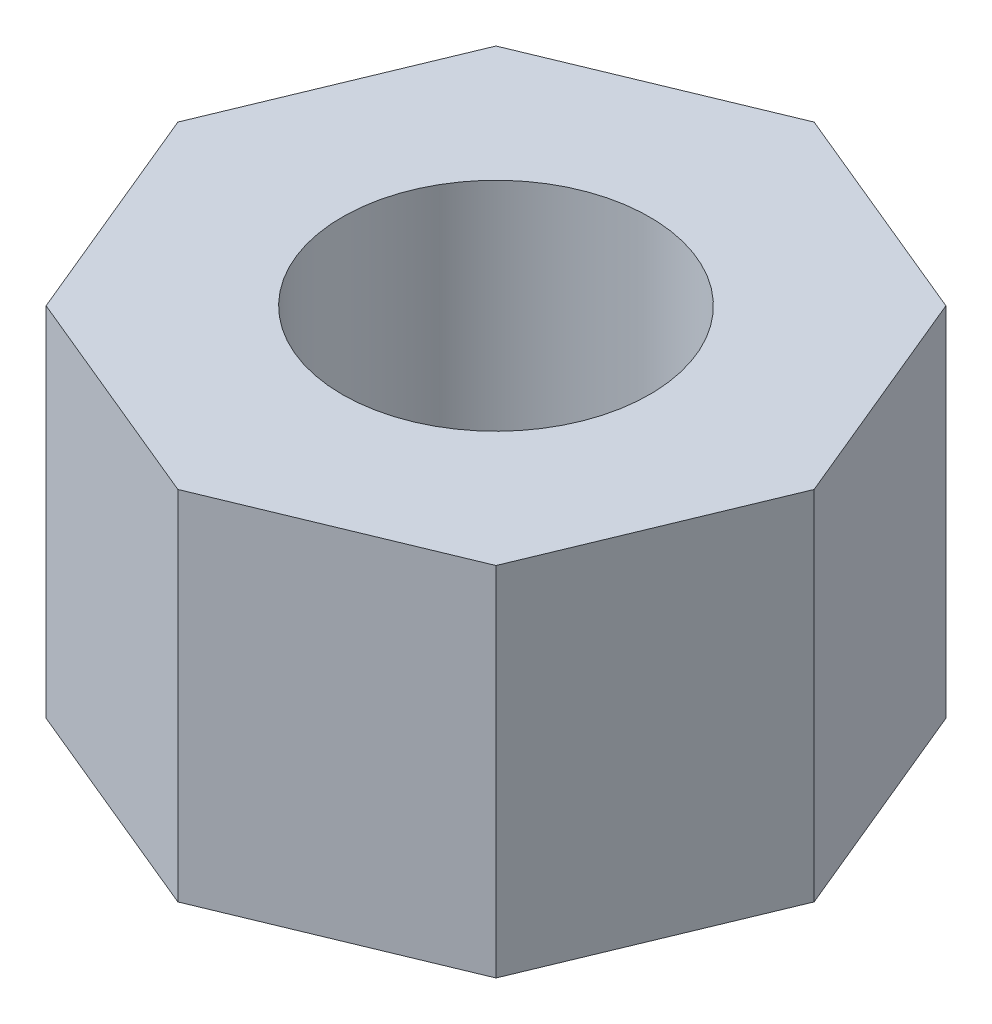
SolidWorks part; units mm, degrees
ref_plane "Front Plane" through (0, 0, 0) normal (0, 0, 1) x (1, 0, 0)
ref_plane "Top Plane" through (0, 0, 0) normal (0, 1, 0) x (1, 0, 0)
ref_plane "Right Plane" through (0, 0, 0) normal (1, 0, 0) x (0, 0, -1)
sketch "Sketch1" plane through (0, 0, 0) normal (0, 1, 0) x (1, 0, 0)
  line L1 (7.0355, 0) -> (4.9749, 4.9749)
  line L2 (4.9749, 4.9749) -> (0, 7.0355)
  line L3 (0, 7.0355) -> (-4.9749, 4.9749)
  line L4 (-4.9749, 4.9749) -> (-7.0355, 0)
  line L5 (-7.0355, 0) -> (-4.9749, -4.9749)
  line L6 (-4.9749, -4.9749) -> (0, -7.0355)
  line L7 (0, -7.0355) -> (4.9749, -4.9749)
  line L8 (4.9749, -4.9749) -> (7.0355, 0)
  circle A0 centre (0, 0) radius 6.5 construction
  circle A1 centre (0, 0) radius 3.4
  dimension "D1" = 13
  dimension "D2" = 6.8
extrude "Boss-Extrude1" add sketch "Sketch1" along normal blind 7.9 contours L7 L8 L1 L2 L3 L4 L5 L6 A1
cosmetic thread "Cosmetic Thread1" parameters "D1"=7.4, "D2"=8
